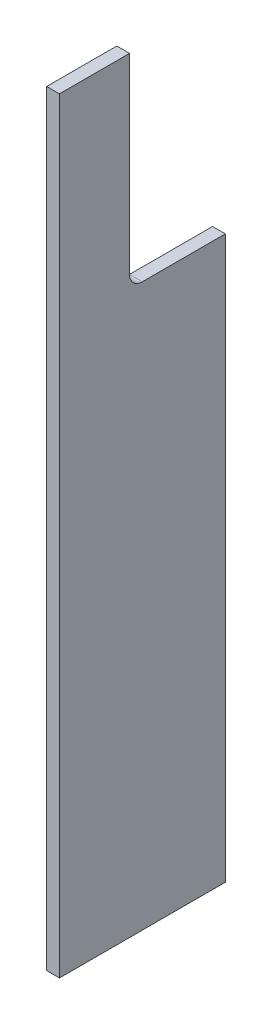
SolidWorks part; units mm, degrees
ref_plane "Plan de face" through (0, 0, 0) normal (0, 0, 1) x (1, 0, 0)
ref_plane "Plan de dessus" through (0, 0, 0) normal (0, 1, 0) x (1, 0, 0)
ref_plane "Plan de droite" through (0, 0, 0) normal (1, 0, 0) x (0, 0, -1)
sketch "Esquisse1" plane through (0, 0, 0) normal (0, 0, 1) x (1, 0, 0)
  line L0 (-91.2495, 0) -> (-222.1354, 0) construction
  line L1 (-155.642, 600) -> (-165.642, 600)
  line L2 (-155.642, 600) -> (-155.642, 0)
  line L3 (-155.642, 0) -> (-165.642, 0)
  line L4 (-165.642, 600) -> (-165.642, 0)
  dimension "D1" = 10
extrude "Boss.-Extru.1" add sketch "Esquisse1" along normal up to surface (129.974 mm away)
sketch "Esquisse2" plane through (-155.642, 0, 0) normal (1, 0, 0) x (0, 0, -1)
  line L0 (0, 0) -> (0, 600) construction
  line L1 (0, 600) -> (-75.046, 600)
  line L2 (0, 600) -> (0, 440)
  line L3 (0, 440) -> (-65.046, 440)
  line L4 (-75.046, 600) -> (-75.046, 450)
  line L5 (-129.974, 600) -> (0, 600) construction
  arc A0 (-65.046, 440) -> (-75.046, 450) centre (-65.046, 450) cw
  dimension "D1" = 10
  dimension "D2" = 150
extrude "Enlèv. mat.-Extru.1" cut sketch "Esquisse2" against normal blind 10
